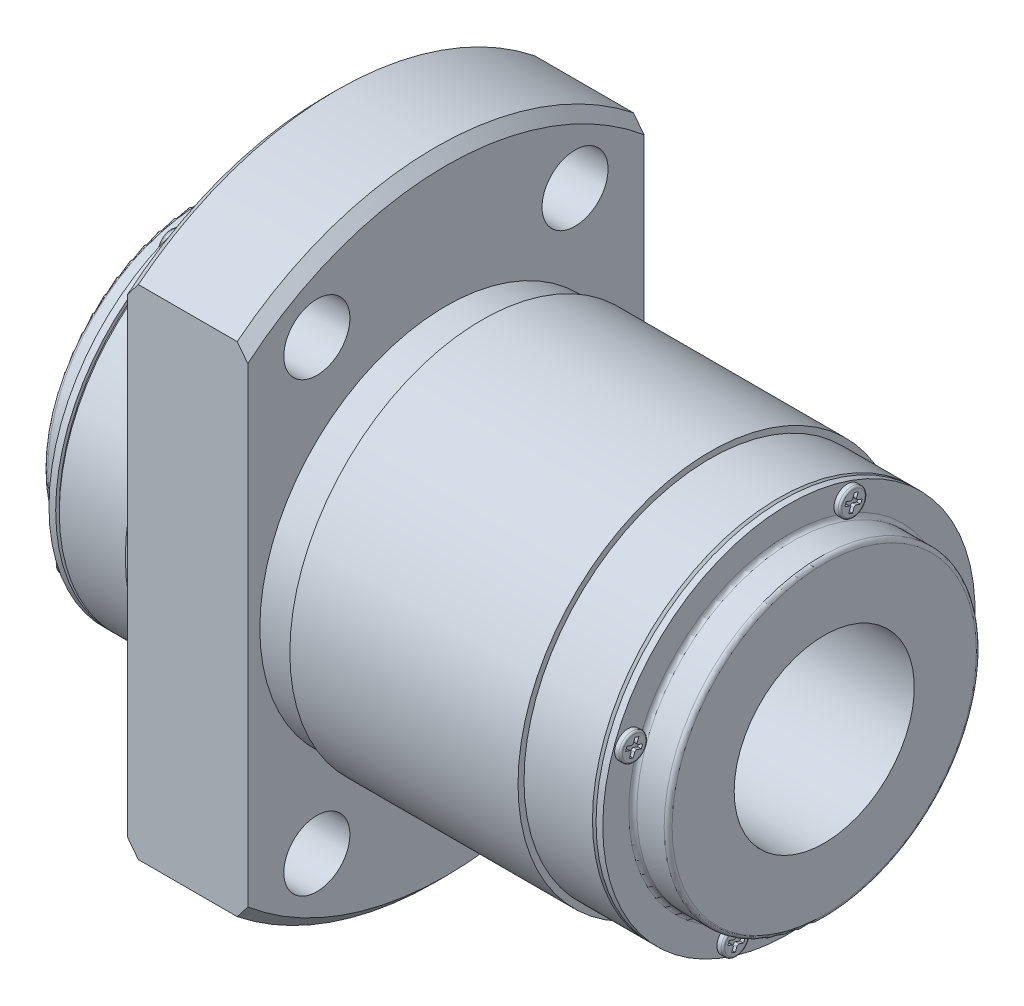
SolidWorks part; units mm, degrees
ref_plane "Front Plane" through (0, 0, 0) normal (0, 0, 1) x (1, 0, 0)
ref_plane "Top Plane" through (0, 0, 0) normal (0, 1, 0) x (1, 0, 0)
ref_plane "Right Plane" through (0, 0, 0) normal (1, 0, 0) x (0, 0, -1)
ref_plane "Plane1" through (0, 0, 0) normal (0, 0, 1) x (1, 0, 0)
sketch "Sketch1" plane through (0, 0, 0) normal (0, 0, 1) x (1, 0, 0)
  line L0 (-3.5, 7.5) -> (48.5, 7.5)
  line L1 (48.5, 7.5) -> (48.5, 12.67)
  line L2 (48.17, 13) -> (45.89, 13)
  line L3 (45.56, 13.33) -> (45.56, 15.5)
  line L4 (45.56, 15.5) -> (45, 15.5)
  line L5 (45, 15.5) -> (45, 15.2)
  line L6 (45, 15.2) -> (44.7, 15.5)
  line L7 (44.7, 15.5) -> (39, 15.5)
  line L8 (39, 15.5) -> (39, 16)
  line L9 (39, 16) -> (20, 16)
  line L10 (20, 16) -> (20, 15.5)
  line L11 (20, 15.5) -> (17, 15.5)
  line L12 (17, 15.5) -> (17, 25.6167)
  line L13 (17, 25.6167) -> (16.1167, 26.5)
  line L14 (16.1167, 26.5) -> (7.8833, 26.5)
  line L15 (7.8833, 26.5) -> (7, 25.6167)
  line L16 (7, 25.6167) -> (7, 16)
  line L17 (7, 16) -> (6.3, 16)
  line L18 (6.3, 16) -> (6.3, 15.5)
  line L19 (6.3, 15.5) -> (0.3, 15.5)
  line L20 (0.3, 15.5) -> (0, 15.2)
  line L21 (0, 15.2) -> (0, 15.5)
  line L22 (0, 15.5) -> (-0.56, 15.5)
  line L23 (-0.56, 15.5) -> (-0.56, 13.33)
  line L24 (-0.89, 13) -> (-3.17, 13)
  line L25 (-3.5, 12.67) -> (-3.5, 7.5)
  line L26 (45, 0) -> (0, 0) construction
  arc A0 (48.5, 12.67) -> (48.17, 13) centre (48.17, 12.67) ccw
  arc A1 (45.89, 13) -> (45.56, 13.33) centre (45.89, 13.33) cw
  arc A2 (-0.56, 13.33) -> (-0.89, 13) centre (-0.89, 13.33) cw
  arc A3 (-3.17, 13) -> (-3.5, 12.67) centre (-3.17, 12.67) ccw
revolve "Revolve1" add sketch "Sketch1" angle 360 about L26
ref_plane "Plane2" through (0, 0, 0) normal (0, -0.5, 0.866) x (1, 0, 0)
sketch "Sketch2" plane through (0, 0, 0) normal (0, -0.5, 0.866) x (1, 0, 0)
  line L0 (7, 21.5) -> (7, 24.25)
  line L1 (7, 24.25) -> (17, 24.25)
  line L2 (17, 24.25) -> (17, 21.5)
  line L3 (17, 21.5) -> (7, 21.5)
  line L4 (17, 21.5) -> (7, 21.5) construction
revolve "Cut-Revolve1" cut sketch "Sketch2" angle 360 about L4
ref_plane "Plane3" through (0, 0, 0) normal (0, -0.5, 0.866) x (1, 0, 0)
sketch "Sketch3" plane through (0, 0, 0) normal (0, -0.5, 0.866) x (1, 0, 0)
  line L0 (7, -21.5) -> (7, -18.75)
  line L1 (7, -18.75) -> (17, -18.75)
  line L2 (17, -18.75) -> (17, -21.5)
  line L3 (17, -21.5) -> (7, -21.5)
  line L4 (17, -21.5) -> (7, -21.5) construction
revolve "Cut-Revolve2" cut sketch "Sketch3" angle 360 about L4
ref_plane "Plane4" through (0, 0, 0) normal (0, 0.5, 0.866) x (1, 0, 0)
sketch "Sketch4" plane through (0, 0, 0) normal (0, 0.5, 0.866) x (1, 0, 0)
  line L0 (7, 21.5) -> (7, 24.25)
  line L1 (7, 24.25) -> (17, 24.25)
  line L2 (17, 24.25) -> (17, 21.5)
  line L3 (17, 21.5) -> (7, 21.5)
  line L4 (17, 21.5) -> (7, 21.5) construction
revolve "Cut-Revolve3" cut sketch "Sketch4" angle 360 about L4
ref_plane "Plane5" through (0, 0, 0) normal (0, 0.5, 0.866) x (1, 0, 0)
sketch "Sketch5" plane through (0, 0, 0) normal (0, 0.5, 0.866) x (1, 0, 0)
  line L0 (7, -21.5) -> (7, -18.75)
  line L1 (7, -18.75) -> (17, -18.75)
  line L2 (17, -18.75) -> (17, -21.5)
  line L3 (17, -21.5) -> (7, -21.5)
  line L4 (17, -21.5) -> (7, -21.5) construction
revolve "Cut-Revolve4" cut sketch "Sketch5" angle 360 about L4
ref_plane "Plane6" through (0, 0, 0) normal (0, 0, 1) x (1, 0, 0)
sketch "Sketch6" plane through (0, 0, 0) normal (0, 0, 1) x (1, 0, 0)
  line L0 (12, -5.5) -> (14.4585, -6.9194)
  line L1 (14.4585, -6.9194) -> (14.4585, -25.9585)
  line L2 (14.4585, -25.9585) -> (15, -26.5)
  line L3 (15, -26.5) -> (12, -26.5)
  line L4 (12, -26.5) -> (12, -5.5)
  line L5 (12, -26.5) -> (12, -5.5) construction
revolve "Cut-Revolve5" cut sketch "Sketch6" angle 360 about L5
ref_plane "Plane7" through (17, 0, 0) normal (1, 0, 0) x (0, 0, -1)
sketch "Sketch7" plane through (17, 0, 0) normal (1, 0, 0) x (0, 0, -1)
  line L0 (-33, 53) -> (-33, -53)
  line L1 (-33, -53) -> (33, -53)
  line L2 (33, -53) -> (33, 53)
  line L3 (33, 53) -> (-33, 53)
  line L4 (-16.5, 27.5) -> (-16.5, -27.5)
  line L5 (-16.5, -27.5) -> (16.5, -27.5)
  line L6 (16.5, -27.5) -> (16.5, 27.5)
  line L7 (16.5, 27.5) -> (-16.5, 27.5)
extrude "Cut-Extrude1" cut sketch "Sketch7" against normal blind 10
ref_plane "Plane8" through (0, 0, 0) normal (0, -0.342, 0.9397) x (1, 0, 0)
sketch "Sketch8" plane through (0, 0, 0) normal (0, -0.342, 0.9397) x (1, 0, 0)
  line L0 (-1.06, 14.25) -> (-1.06, 15.17)
  line L1 (-0.86, 15.37) -> (-0.56, 15.37)
  line L2 (-0.56, 15.37) -> (-0.56, 14.25)
  line L3 (-0.56, 14.25) -> (-1.06, 14.25)
  line L4 (-0.56, 14.25) -> (-1.06, 14.25) construction
  arc A0 (-1.06, 15.17) -> (-0.86, 15.37) centre (-0.86, 15.17) cw
revolve "Revolve2" add sketch "Sketch8" angle 360 about L4
ref_plane "Plane9" through (0, -4.8738, 13.3906) normal (0, -0.342, 0.9397) x (1, 0, 0)
sketch "Sketch9" plane through (0, -4.8738, 13.3906) normal (0, -0.342, 0.9397) x (1, 0, 0)
  line L0 (-1.06, 0) -> (-1.06, 0.92)
  line L1 (-0.86, 1.12) -> (-0.56, 1.12)
  line L2 (-0.56, 1.12) -> (-0.56, 0)
  line L3 (-0.56, 0) -> (-1.06, 0)
  line L4 (-0.56, 0) -> (-1.06, 0) construction
  arc A0 (-1.06, 0.92) -> (-0.86, 1.12) centre (-0.86, 0.92) cw
revolve "Revolve3" add sketch "Sketch9" angle 360 about L4
ref_plane "Plane10" through (0, 0, 0) normal (0, -0.342, 0.9397) x (1, 0, 0)
sketch "Sketch10" plane through (0, 0, 0) normal (0, -0.342, 0.9397) x (1, 0, 0)
  line L0 (-1.06, -14.25) -> (-1.06, -13.33)
  line L1 (-0.86, -13.13) -> (-0.56, -13.13)
  line L2 (-0.56, -13.13) -> (-0.56, -14.25)
  line L3 (-0.56, -14.25) -> (-1.06, -14.25)
  line L4 (-0.56, -14.25) -> (-1.06, -14.25) construction
  arc A0 (-1.06, -13.33) -> (-0.86, -13.13) centre (-0.86, -13.33) cw
revolve "Revolve4" add sketch "Sketch10" angle 360 about L4
ref_plane "Plane11" through (0, 4.8738, -13.3906) normal (0, -0.342, 0.9397) x (1, 0, 0)
sketch "Sketch11" plane through (0, 4.8738, -13.3906) normal (0, -0.342, 0.9397) x (1, 0, 0)
  line L0 (-1.06, 0) -> (-1.06, 0.92)
  line L1 (-0.86, 1.12) -> (-0.56, 1.12)
  line L2 (-0.56, 1.12) -> (-0.56, 0)
  line L3 (-0.56, 0) -> (-1.06, 0)
  line L4 (-0.56, 0) -> (-1.06, 0) construction
  arc A0 (-1.06, 0.92) -> (-0.86, 1.12) centre (-0.86, 0.92) cw
revolve "Revolve5" add sketch "Sketch11" angle 360 about L4
ref_plane "Plane12" through (0, 0, 0) normal (0, 0.342, 0.9397) x (1, 0, 0)
sketch "Sketch12" plane through (0, 0, 0) normal (0, 0.342, 0.9397) x (1, 0, 0)
  line L0 (45.56, 14.25) -> (45.56, 15.37)
  line L1 (45.56, 15.37) -> (45.91, 15.37)
  line L2 (46.06, 15.22) -> (46.06, 14.25)
  line L3 (46.06, 14.25) -> (45.56, 14.25)
  line L4 (46.06, 14.25) -> (45.56, 14.25) construction
  arc A0 (45.91, 15.37) -> (46.06, 15.22) centre (45.91, 15.22) cw
revolve "Revolve6" add sketch "Sketch12" angle 360 about L4
ref_plane "Plane13" through (0, -4.8738, -13.3906) normal (0, 0.342, 0.9397) x (1, 0, 0)
sketch "Sketch13" plane through (0, -4.8738, -13.3906) normal (0, 0.342, 0.9397) x (1, 0, 0)
  line L0 (45.56, 0) -> (45.56, 1.12)
  line L1 (45.56, 1.12) -> (45.91, 1.12)
  line L2 (46.06, 0.97) -> (46.06, 0)
  line L3 (46.06, 0) -> (45.56, 0)
  line L4 (46.06, 0) -> (45.56, 0) construction
  arc A0 (45.91, 1.12) -> (46.06, 0.97) centre (45.91, 0.97) cw
revolve "Revolve7" add sketch "Sketch13" angle 360 about L4
ref_plane "Plane14" through (0, 0, 0) normal (0, 0.342, 0.9397) x (1, 0, 0)
sketch "Sketch14" plane through (0, 0, 0) normal (0, 0.342, 0.9397) x (1, 0, 0)
  line L0 (45.56, -14.25) -> (45.56, -13.13)
  line L1 (45.56, -13.13) -> (45.91, -13.13)
  line L2 (46.06, -13.28) -> (46.06, -14.25)
  line L3 (46.06, -14.25) -> (45.56, -14.25)
  line L4 (46.06, -14.25) -> (45.56, -14.25) construction
  arc A0 (45.91, -13.13) -> (46.06, -13.28) centre (45.91, -13.28) cw
revolve "Revolve8" add sketch "Sketch14" angle 360 about L4
ref_plane "Plane15" through (0, 4.8738, 13.3906) normal (0, 0.342, 0.9397) x (1, 0, 0)
sketch "Sketch15" plane through (0, 4.8738, 13.3906) normal (0, 0.342, 0.9397) x (1, 0, 0)
  line L0 (45.56, 0) -> (45.56, 1.12)
  line L1 (45.56, 1.12) -> (45.91, 1.12)
  line L2 (46.06, 0.97) -> (46.06, 0)
  line L3 (46.06, 0) -> (45.56, 0)
  line L4 (46.06, 0) -> (45.56, 0) construction
  arc A0 (45.91, 1.12) -> (46.06, 0.97) centre (45.91, 0.97) cw
revolve "Revolve9" add sketch "Sketch15" angle 360 about L4
ref_plane "Plane16" through (46.06, 0, 0) normal (1, 0, 0) x (0, 0, -1)
sketch "Sketch16" plane through (46.06, 0, 0) normal (1, 0, 0) x (0, 0, -1)
  line L0 (4.1643, 13.4733) -> (4.512, 13.3467)
  line L1 (4.6076, 13.1417) -> (4.481, 12.794)
  line L2 (4.481, 12.794) -> (4.7911, 12.6811)
  line L3 (4.7911, 12.6811) -> (4.9177, 13.0288)
  line L4 (5.1228, 13.1244) -> (5.4704, 12.9979)
  line L5 (5.4704, 12.9979) -> (5.5833, 13.308)
  line L6 (5.5833, 13.308) -> (5.2356, 13.4345)
  line L7 (5.14, 13.6396) -> (5.2665, 13.9873)
  line L8 (5.2665, 13.9873) -> (4.9564, 14.1001)
  line L9 (4.9564, 14.1001) -> (4.8299, 13.7525)
  line L10 (4.6248, 13.6568) -> (4.2771, 13.7834)
  line L11 (4.2771, 13.7834) -> (4.1643, 13.4733)
  arc A0 (4.512, 13.3467) -> (4.6076, 13.1417) centre (4.4572, 13.1964) cw
  arc A1 (4.9177, 13.0288) -> (5.1228, 13.1244) centre (5.068, 12.9741) cw
  arc A2 (5.2356, 13.4345) -> (5.14, 13.6396) centre (5.2903, 13.5849) cw
  arc A3 (4.8299, 13.7525) -> (4.6248, 13.6568) centre (4.6795, 13.8072) cw
extrude "Cut-Extrude2" cut sketch "Sketch16" against normal blind 0.3
ref_plane "Plane17" through (46.06, 0, 0) normal (1, 0, 0) x (0, 0, -1)
sketch "Sketch17" plane through (46.06, 0, 0) normal (1, 0, 0) x (0, 0, -1)
  line L0 (-14.1001, 4.9564) -> (-13.7525, 4.8299)
  line L1 (-13.6568, 4.6248) -> (-13.7834, 4.2771)
  line L2 (-13.7834, 4.2771) -> (-13.4733, 4.1643)
  line L3 (-13.4733, 4.1643) -> (-13.3467, 4.512)
  line L4 (-13.1417, 4.6076) -> (-12.794, 4.481)
  line L5 (-12.794, 4.481) -> (-12.6811, 4.7911)
  line L6 (-12.6811, 4.7911) -> (-13.0288, 4.9177)
  line L7 (-13.1244, 5.1228) -> (-12.9979, 5.4704)
  line L8 (-12.9979, 5.4704) -> (-13.308, 5.5833)
  line L9 (-13.308, 5.5833) -> (-13.4345, 5.2356)
  line L10 (-13.6396, 5.14) -> (-13.9873, 5.2665)
  line L11 (-13.9873, 5.2665) -> (-14.1001, 4.9564)
  arc A0 (-13.7525, 4.8299) -> (-13.6568, 4.6248) centre (-13.8072, 4.6795) cw
  arc A1 (-13.3467, 4.512) -> (-13.1417, 4.6076) centre (-13.1964, 4.4572) cw
  arc A2 (-13.0288, 4.9177) -> (-13.1244, 5.1228) centre (-12.9741, 5.068) cw
  arc A3 (-13.4345, 5.2356) -> (-13.6396, 5.14) centre (-13.5849, 5.2903) cw
extrude "Cut-Extrude3" cut sketch "Sketch17" against normal blind 0.3
ref_plane "Plane18" through (46.06, 0, 0) normal (1, 0, 0) x (0, 0, -1)
sketch "Sketch18" plane through (46.06, 0, 0) normal (1, 0, 0) x (0, 0, -1)
  line L0 (-5.5833, -13.308) -> (-5.2356, -13.4345)
  line L1 (-5.14, -13.6396) -> (-5.2665, -13.9873)
  line L2 (-5.2665, -13.9873) -> (-4.9564, -14.1001)
  line L3 (-4.9564, -14.1001) -> (-4.8299, -13.7525)
  line L4 (-4.6248, -13.6568) -> (-4.2771, -13.7834)
  line L5 (-4.2771, -13.7834) -> (-4.1643, -13.4733)
  line L6 (-4.1643, -13.4733) -> (-4.512, -13.3467)
  line L7 (-4.6076, -13.1417) -> (-4.481, -12.794)
  line L8 (-4.481, -12.794) -> (-4.7911, -12.6811)
  line L9 (-4.7911, -12.6811) -> (-4.9177, -13.0288)
  line L10 (-5.1228, -13.1244) -> (-5.4704, -12.9979)
  line L11 (-5.4704, -12.9979) -> (-5.5833, -13.308)
  arc A0 (-5.2356, -13.4345) -> (-5.14, -13.6396) centre (-5.2903, -13.5849) cw
  arc A1 (-4.8299, -13.7525) -> (-4.6248, -13.6568) centre (-4.6795, -13.8072) cw
  arc A2 (-4.512, -13.3467) -> (-4.6076, -13.1417) centre (-4.4572, -13.1964) cw
  arc A3 (-4.9177, -13.0288) -> (-5.1228, -13.1244) centre (-5.068, -12.9741) cw
extrude "Cut-Extrude4" cut sketch "Sketch18" against normal blind 0.3
ref_plane "Plane19" through (46.06, 0, 0) normal (1, 0, 0) x (0, 0, -1)
sketch "Sketch19" plane through (46.06, 0, 0) normal (1, 0, 0) x (0, 0, -1)
  line L0 (12.6811, -4.7911) -> (13.0288, -4.9177)
  line L1 (13.1244, -5.1228) -> (12.9979, -5.4704)
  line L2 (12.9979, -5.4704) -> (13.308, -5.5833)
  line L3 (13.308, -5.5833) -> (13.4345, -5.2356)
  line L4 (13.6396, -5.14) -> (13.9873, -5.2665)
  line L5 (13.9873, -5.2665) -> (14.1001, -4.9564)
  line L6 (14.1001, -4.9564) -> (13.7525, -4.8299)
  line L7 (13.6568, -4.6248) -> (13.7834, -4.2771)
  line L8 (13.7834, -4.2771) -> (13.4733, -4.1643)
  line L9 (13.4733, -4.1643) -> (13.3467, -4.512)
  line L10 (13.1417, -4.6076) -> (12.794, -4.481)
  line L11 (12.794, -4.481) -> (12.6811, -4.7911)
  arc A0 (13.0288, -4.9177) -> (13.1244, -5.1228) centre (12.9741, -5.068) cw
  arc A1 (13.4345, -5.2356) -> (13.6396, -5.14) centre (13.5849, -5.2903) cw
  arc A2 (13.7525, -4.8299) -> (13.6568, -4.6248) centre (13.8072, -4.6795) cw
  arc A3 (13.3467, -4.512) -> (13.1417, -4.6076) centre (13.1964, -4.4572) cw
extrude "Cut-Extrude5" cut sketch "Sketch19" against normal blind 0.3
ref_plane "Plane20" through (-1.06, 0, 0) normal (1, 0, 0) x (0, 0, -1)
sketch "Sketch20" plane through (-1.06, 0, 0) normal (1, 0, 0) x (0, 0, -1)
  line L0 (-5.5833, 13.308) -> (-5.4704, 12.9979)
  line L1 (-5.4704, 12.9979) -> (-5.1228, 13.1244)
  line L2 (-4.9177, 13.0288) -> (-4.7911, 12.6811)
  line L3 (-4.7911, 12.6811) -> (-4.481, 12.794)
  line L4 (-4.481, 12.794) -> (-4.6076, 13.1417)
  line L5 (-4.512, 13.3467) -> (-4.1643, 13.4733)
  line L6 (-4.1643, 13.4733) -> (-4.2771, 13.7834)
  line L7 (-4.2771, 13.7834) -> (-4.6248, 13.6568)
  line L8 (-4.8299, 13.7525) -> (-4.9564, 14.1001)
  line L9 (-4.9564, 14.1001) -> (-5.2665, 13.9873)
  line L10 (-5.2665, 13.9873) -> (-5.14, 13.6396)
  line L11 (-5.2356, 13.4345) -> (-5.5833, 13.308)
  arc A0 (-5.1228, 13.1244) -> (-4.9177, 13.0288) centre (-5.068, 12.9741) cw
  arc A1 (-4.6076, 13.1417) -> (-4.512, 13.3467) centre (-4.4572, 13.1964) cw
  arc A2 (-4.6248, 13.6568) -> (-4.8299, 13.7525) centre (-4.6795, 13.8072) cw
  arc A3 (-5.14, 13.6396) -> (-5.2356, 13.4345) centre (-5.2903, 13.5849) cw
extrude "Cut-Extrude6" cut sketch "Sketch20" along normal blind 0.3
ref_plane "Plane21" through (-1.06, 0, 0) normal (1, 0, 0) x (0, 0, -1)
sketch "Sketch21" plane through (-1.06, 0, 0) normal (1, 0, 0) x (0, 0, -1)
  line L0 (-14.1001, -4.9564) -> (-13.9873, -5.2665)
  line L1 (-13.9873, -5.2665) -> (-13.6396, -5.14)
  line L2 (-13.4345, -5.2356) -> (-13.308, -5.5833)
  line L3 (-13.308, -5.5833) -> (-12.9979, -5.4704)
  line L4 (-12.9979, -5.4704) -> (-13.1244, -5.1228)
  line L5 (-13.0288, -4.9177) -> (-12.6811, -4.7911)
  line L6 (-12.6811, -4.7911) -> (-12.794, -4.481)
  line L7 (-12.794, -4.481) -> (-13.1417, -4.6076)
  line L8 (-13.3467, -4.512) -> (-13.4733, -4.1643)
  line L9 (-13.4733, -4.1643) -> (-13.7834, -4.2771)
  line L10 (-13.7834, -4.2771) -> (-13.6568, -4.6248)
  line L11 (-13.7525, -4.8299) -> (-14.1001, -4.9564)
  arc A0 (-13.6396, -5.14) -> (-13.4345, -5.2356) centre (-13.5849, -5.2903) cw
  arc A1 (-13.1244, -5.1228) -> (-13.0288, -4.9177) centre (-12.9741, -5.068) cw
  arc A2 (-13.1417, -4.6076) -> (-13.3467, -4.512) centre (-13.1964, -4.4572) cw
  arc A3 (-13.6568, -4.6248) -> (-13.7525, -4.8299) centre (-13.8072, -4.6795) cw
extrude "Cut-Extrude7" cut sketch "Sketch21" along normal blind 0.3
ref_plane "Plane22" through (-1.06, 0, 0) normal (1, 0, 0) x (0, 0, -1)
sketch "Sketch22" plane through (-1.06, 0, 0) normal (1, 0, 0) x (0, 0, -1)
  line L0 (4.1643, -13.4733) -> (4.2771, -13.7834)
  line L1 (4.2771, -13.7834) -> (4.6248, -13.6568)
  line L2 (4.8299, -13.7525) -> (4.9564, -14.1001)
  line L3 (4.9564, -14.1001) -> (5.2665, -13.9873)
  line L4 (5.2665, -13.9873) -> (5.14, -13.6396)
  line L5 (5.2356, -13.4345) -> (5.5833, -13.308)
  line L6 (5.5833, -13.308) -> (5.4704, -12.9979)
  line L7 (5.4704, -12.9979) -> (5.1228, -13.1244)
  line L8 (4.9177, -13.0288) -> (4.7911, -12.6811)
  line L9 (4.7911, -12.6811) -> (4.481, -12.794)
  line L10 (4.481, -12.794) -> (4.6076, -13.1417)
  line L11 (4.512, -13.3467) -> (4.1643, -13.4733)
  arc A0 (4.6248, -13.6568) -> (4.8299, -13.7525) centre (4.6795, -13.8072) cw
  arc A1 (5.14, -13.6396) -> (5.2356, -13.4345) centre (5.2903, -13.5849) cw
  arc A2 (5.1228, -13.1244) -> (4.9177, -13.0288) centre (5.068, -12.9741) cw
  arc A3 (4.6076, -13.1417) -> (4.512, -13.3467) centre (4.4572, -13.1964) cw
extrude "Cut-Extrude8" cut sketch "Sketch22" along normal blind 0.3
ref_plane "Plane23" through (-1.06, 0, 0) normal (1, 0, 0) x (0, 0, -1)
sketch "Sketch23" plane through (-1.06, 0, 0) normal (1, 0, 0) x (0, 0, -1)
  line L0 (12.6811, 4.7911) -> (12.794, 4.481)
  line L1 (12.794, 4.481) -> (13.1417, 4.6076)
  line L2 (13.3467, 4.512) -> (13.4733, 4.1643)
  line L3 (13.4733, 4.1643) -> (13.7834, 4.2771)
  line L4 (13.7834, 4.2771) -> (13.6568, 4.6248)
  line L5 (13.7525, 4.8299) -> (14.1001, 4.9564)
  line L6 (14.1001, 4.9564) -> (13.9873, 5.2665)
  line L7 (13.9873, 5.2665) -> (13.6396, 5.14)
  line L8 (13.4345, 5.2356) -> (13.308, 5.5833)
  line L9 (13.308, 5.5833) -> (12.9979, 5.4704)
  line L10 (12.9979, 5.4704) -> (13.1244, 5.1228)
  line L11 (13.0288, 4.9177) -> (12.6811, 4.7911)
  arc A0 (13.1417, 4.6076) -> (13.3467, 4.512) centre (13.1964, 4.4572) cw
  arc A1 (13.6568, 4.6248) -> (13.7525, 4.8299) centre (13.8072, 4.6795) cw
  arc A2 (13.6396, 5.14) -> (13.4345, 5.2356) centre (13.5849, 5.2903) cw
  arc A3 (13.1244, 5.1228) -> (13.0288, 4.9177) centre (12.9741, 5.068) cw
extrude "Cut-Extrude9" cut sketch "Sketch23" along normal blind 0.3
